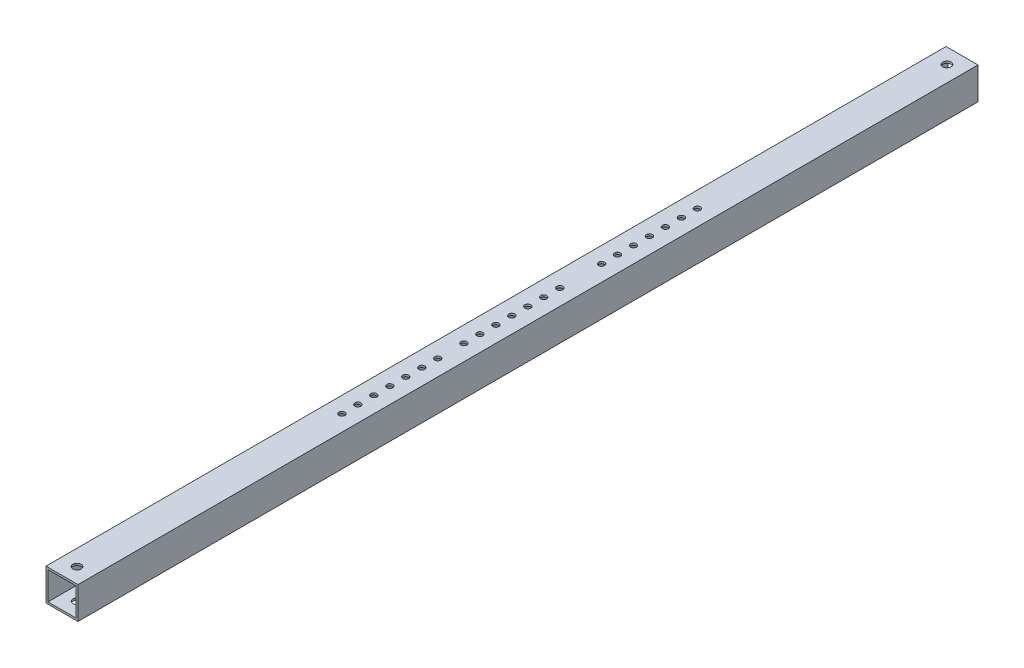
SolidWorks part; units mm, degrees
material "ALUMINUM 6061-T6"
ref_plane "Front Plane" through (0, 0, 0) normal (0, 0, 1) x (1, 0, 0)
ref_plane "Top Plane" through (0, 0, 0) normal (0, 1, 0) x (1, 0, 0)
ref_plane "Right Plane" through (0, 0, 0) normal (1, 0, 0) x (0, 0, -1)
sketch "Sketch1" plane through (0, 0, 0) normal (0, 0, 1) x (1, 0, 0)
  line L0 (11.1125, -11.1125) -> (11.1125, 11.1125)
  line L1 (-12.7, -12.7) -> (12.7, -12.7)
  line L2 (-12.7, -12.7) -> (-12.7, 12.7)
  line L3 (-12.7, 12.7) -> (12.7, 12.7)
  line L4 (12.7, -12.7) -> (12.7, 12.7)
  line L5 (-12.7, -12.7) -> (12.7, 12.7) construction
  line L6 (-12.7, 12.7) -> (12.7, -12.7) construction
  line L7 (-11.1125, 11.1125) -> (11.1125, 11.1125)
  line L8 (-11.1125, -11.1125) -> (-11.1125, 11.1125)
  line L9 (-11.1125, -11.1125) -> (11.1125, -11.1125)
  point P0 (0, 0)
  dimension "D1" = 25.4
  dimension "D2" = 25.4
  dimension "D3" = 1.5875
extrude "Boss-Extrude1" add sketch "Sketch1" along normal mid plane 715.518
sketch "Sketch2" plane through (0, -12.7, 0) normal (0, -1, 0) x (1, 0, 0)
  line L0 (-12.7, 357.759) -> (12.7, 357.759) construction
  circle A0 centre (0, -37.973) radius 2.3812
  circle A1 centre (0, -25.273) radius 2.3812
  circle A2 centre (0, -12.573) radius 2.3812
  circle A3 centre (0, 0.127) radius 2.3812
  circle A4 centre (0, 12.827) radius 2.3812
  circle A5 centre (0, 25.527) radius 2.3812
  circle A6 centre (0, 38.227) radius 2.3812
  dimension "D1" = 4.7625
  dimension "D2" = 12.7
  dimension "D3" = 12.7
  dimension "D4" = 12.7
  dimension "D5" = 12.7
  dimension "D6" = 12.7
  dimension "D7" = 12.7
  dimension "D8" = 357.632
extrude "Cut-Extrude1" cut sketch "Sketch2" against normal through all
sketch "Sketch3" plane through (0, -12.7, 0) normal (0, -1, 0) x (1, 0, 0)
  line L1 (-12.7, -357.759) -> (12.7, -357.759) construction
  circle A0 centre (0, 59.0186) radius 2.3812
  circle A1 centre (0, 71.7186) radius 2.3812
  circle A2 centre (0, 84.4186) radius 2.3812
  circle A3 centre (0, 109.8186) radius 2.3812
  circle A4 centre (0, 122.5186) radius 2.3812
  circle A5 centre (0, 135.2186) radius 2.3812
  circle A6 centre (0, 97.1186) radius 2.3812
  circle A7 centre (0, -71.1814) radius 2.3812
  circle A8 centre (0, -83.8814) radius 2.3812
  circle A9 centre (0, -96.5814) radius 2.3812
  circle A10 centre (0, -109.2814) radius 2.3812
  circle A11 centre (0, -121.9814) radius 2.3812
  circle A12 centre (0, -134.6814) radius 2.3812
  circle A13 centre (0, -147.3814) radius 2.3812
  dimension "D1" = 4.7625
  dimension "D9" = 4.7625
  dimension "D10" = 12.7
  dimension "D11" = 12.7
  dimension "D12" = 12.7
  dimension "D13" = 12.7
  dimension "D14" = 12.7
  dimension "D15" = 12.7
  dimension "D16" = 454.8776
  dimension "D8" = 248.4776
  dimension "D2" = 12.7
  dimension "D3" = 12.7
  dimension "D4" = 12.7
  dimension "D5" = 12.7
  dimension "D6" = 12.7
  dimension "D7" = 12.7
extrude "Cut-Extrude2" cut sketch "Sketch3" against normal through all
hole_wizard "M6 Clearance Hole1" positions "Sketch5" profile "Sketch4" hole size "M6" standard "ANSI Metric" end condition through all
sketch "Sketch5" plane through (0, -12.7, 0) normal (0, -1, 0) x (-1, 0, 0)
  line L0 (12.7, 357.759) -> (-12.7, 357.759) construction
  line L1 (12.7, -357.759) -> (-12.7, -357.759) construction
  point P0 (0, -345.759)
  point P2 (0, 345.759)
  dimension "D1" = 12
  dimension "D2" = 12
sketch "Sketch4" plane through (0, -12.7, 345.759) normal (1, 0, 0) x (0, 0, -1)
  line L0 (0, 0) -> (0, 25.4)
  line L1 (0, 25.4) -> (3.3, 25.4)
  line L2 (3.3, 25.4) -> (3.3, 0)
  line L5 (3.3, 0) -> (0, 0)
  line L11 (0, -6.35) -> (0, 107.95) construction
  dimension "Thru Hole Dia." = 6.6
  dimension "Thru Hole Depth" = 25.4
